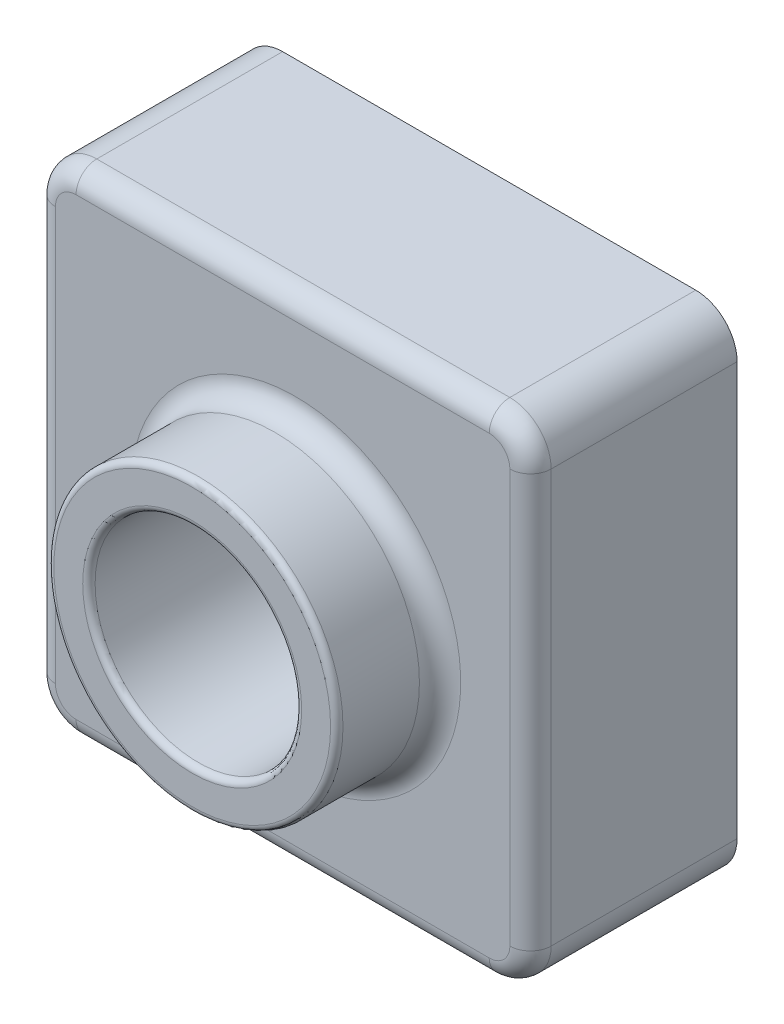
SolidWorks part; units mm, degrees
material "Chrome Stainless Steel"
ref_plane "Front" through (0, 0, 0) normal (0, 0, 1) x (1, 0, 0)
ref_plane "Top" through (0, 0, 0) normal (0, 1, 0) x (1, 0, 0)
ref_plane "Right" through (0, 0, 0) normal (1, 0, 0) x (0, 0, -1)
sketch "Sketch1" plane through (0, 0, 0) normal (0, 0, 1) x (1, 0, 0)
  line L1 (0, 0) -> (120, 0)
  line L2 (0, 0) -> (0, 120)
  line L3 (0, 120) -> (120, 120)
  line L4 (120, 0) -> (120, 120)
  dimension "D1" = 120
  dimension "D2" = 120
extrude "Boss-Extrude1" add sketch "Sketch1" along normal blind 50
sketch "Sketch2" plane through (0, 0, 50) normal (0, 0, 1) x (1, 0, 0)
  circle A0 centre (63.105, 59.2607) radius 35
  dimension "D1" = 70
extrude "Boss-Extrude2" add sketch "Sketch2" along normal blind 25
sketch "Sketch3" plane through (0, 0, 75) normal (0, 0, 1) x (1, 0, 0)
  circle A0 centre (63.105, 59.2607) radius 25
  dimension "D1" = 50
extrude "Cut-Extrude1" cut sketch "Sketch3" against normal through all
fillet "Fillet1" radius 10 4 edges at (0, 0, 25) (0, 120, 25) (120, 0, 25) (120, 120, 25)
fillet "Fillet5" radius 1.5 2 edges at (98.105, 59.2607, 75) (88.105, 59.2607, 75)
fillet "Fillet6" radius 5 9 edges at (28.105, 59.2607, 50) (2.9289, 117.0711, 50) (60, 120, 50) (117.0711, 117.0711, 50) (120, 60, 50) (117.0711, 2.9289, 50) (60, 0, 50) (2.9289, 2.9289, 50) (0, 60, 50)
shell "Shell1" thickness 2
